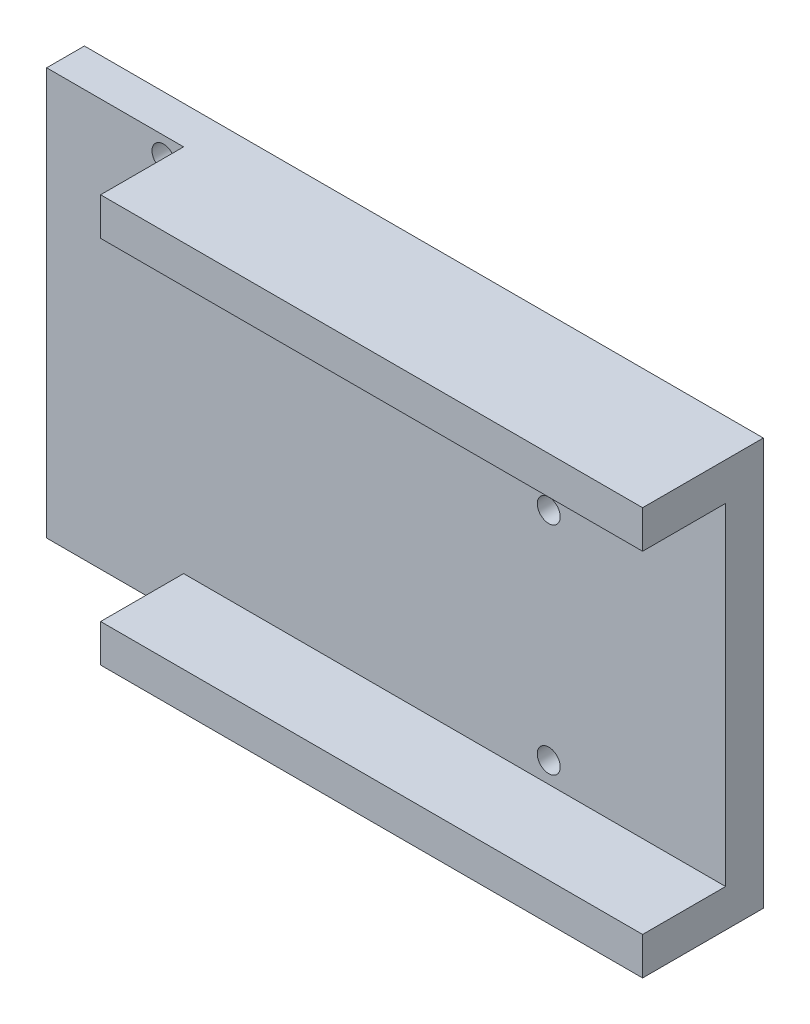
SolidWorks part; units mm, degrees
ref_plane "前视基准面" through (0, 0, 0) normal (0, 0, 1) x (1, 0, 0)
ref_plane "上视基准面" through (0, 0, 0) normal (0, 1, 0) x (1, 0, 0)
ref_plane "右视基准面" through (0, 0, 0) normal (1, 0, 0) x (0, 0, -1)
other "Configuration Table"
sketch "草图1" plane through (0, 0, 0) normal (0, 0, 1) x (1, 0, 0)
  line L0 (-120.576, -480.7836) -> (-20.6014, -480.7836) construction
  line L1 (-120.576, -480.7836) -> (-30.6014, -480.7836)
  line L2 (-120.576, -480.7836) -> (-120.576, -534.7582)
  line L3 (-120.576, -534.7582) -> (-30.6014, -534.7582)
  line L4 (-30.6014, -480.7836) -> (-30.6014, -534.7582)
  line L6 (-20.6014, -480.7836) -> (-20.6014, -534.7582) construction
  line L7 (-20.6014, -534.7582) -> (-120.576, -534.7582) construction
  dimension "D1" = 10
extrude "凸台-拉伸1" add sketch "草图1" against normal blind 16
shell "抽壳1" thickness 5
sketch "草图2" plane through (-120.576, 0, 0) normal (-1, 0, 0) x (0, 0, 1)
  line L0 (0, -480.7836) -> (0, -534.7582) construction
  line L1 (0, -485.7836) -> (-11, -485.7836)
  line L2 (0, -485.7836) -> (0, -529.7582)
  line L3 (0, -529.7582) -> (-11, -529.7582)
  line L4 (-11, -485.7836) -> (-11, -529.7582)
  line L5 (-16, -480.7836) -> (0, -480.7836) construction
  line L6 (-16, -480.7836) -> (-16, -534.7582) construction
  line L7 (-16, -534.7582) -> (0, -534.7582) construction
  dimension "D1" = 5
  dimension "D2" = 5
  dimension "D3" = 5
extrude "切除-拉伸1" cut sketch "草图2" against normal through all
sketch "草图3" plane through (0, -534.7582, 0) normal (0, -1, 0) x (1, 0, 0)
  line L0 (-102.4277, 0) -> (-102.4277, -11)
  line L1 (-30.6014, 0) -> (-120.576, 0) construction
  line L2 (-102.4277, 0) -> (-102.4277, 1.6) construction
  line L4 (-120.576, -11) -> (-120.576, 0) construction
  line L5 (-120.576, -11) -> (-120.576, 0) construction
  line L6 (-120.576, -11) -> (-102.4277, -11)
  line L7 (-120.576, -11) -> (-120.576, 0)
  line L8 (-120.576, 0) -> (-102.4277, 0)
extrude "切除-拉伸2" cut sketch "草图3" against normal through all
sketch "草图4" plane through (0, 0, 0) normal (0, 0, 1) x (1, 0, 0)
  circle A0 centre (-105.0926, -483.3109) radius 1.524
  circle A1 centre (-54.0385, -526.999) radius 1.524
  circle A2 centre (-54.0385, -498.297) radius 1.524
extrude "切除-拉伸3" cut sketch "草图4" against normal through all
ref_plane "基准面1" through (0, 0, -16) normal (0, 0, -1) x (-1, 0, 0)
ref_plane "基准面2" through (0, -480.7836, 0) normal (0, 1, 0) x (1, 0, 0)
